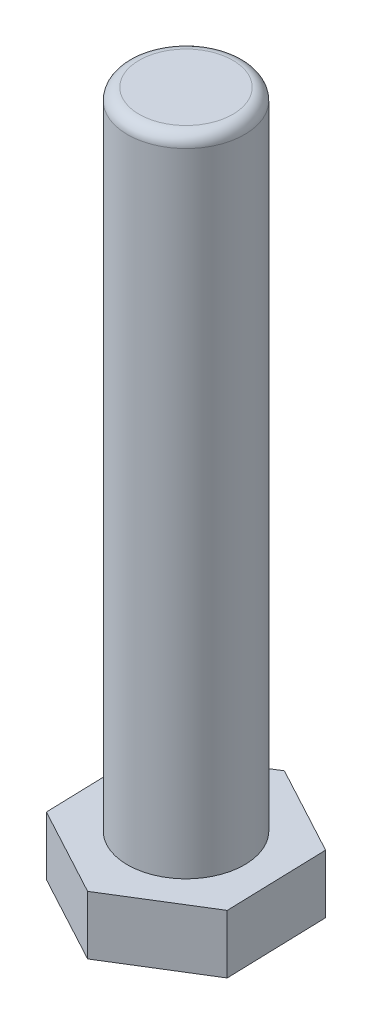
SolidWorks part; units mm, degrees
ref_plane "Plan de face" through (0, 0, 0) normal (0, 0, 1) x (1, 0, 0)
ref_plane "Plan de dessus" through (0, 0, 0) normal (0, 1, 0) x (1, 0, 0)
ref_plane "Plan de droite" through (0, 0, 0) normal (1, 0, 0) x (0, 0, -1)
sketch "Esquisse1" plane through (0, 0, 0) normal (0, 1, 0) x (1, 0, 0)
  line L0 (14.7363, 9.1018) -> (-0.5143, 17.3129)
  line L1 (-14.7363, -9.1018) -> (0.5143, -17.3129)
  line L2 (0.5143, -17.3129) -> (15.2505, -8.2111)
  line L3 (15.2505, -8.2111) -> (14.7363, 9.1018)
  line L4 (-0.5143, 17.3129) -> (-15.2505, 8.2111)
  line L5 (-15.2505, 8.2111) -> (-14.7363, -9.1018)
  circle A0 centre (0, 0) radius 15 construction
  dimension "D1" = 30
extrude "Boss.-Extru.1" add sketch "Esquisse1" along normal blind 10
sketch "Esquisse2" plane through (0, 10, 0) normal (0, 1, 0) x (1, 0, 0)
  circle A0 centre (0, 0) radius 10
extrude "Boss.-Extru.2" add sketch "Esquisse2" along normal blind 110
cosmetic thread "Représentation de filetage1" parameters "D1"=40, "D2"=6.619
fillet "Congé1" radius 2 1 edges at (0, 120, 10)
